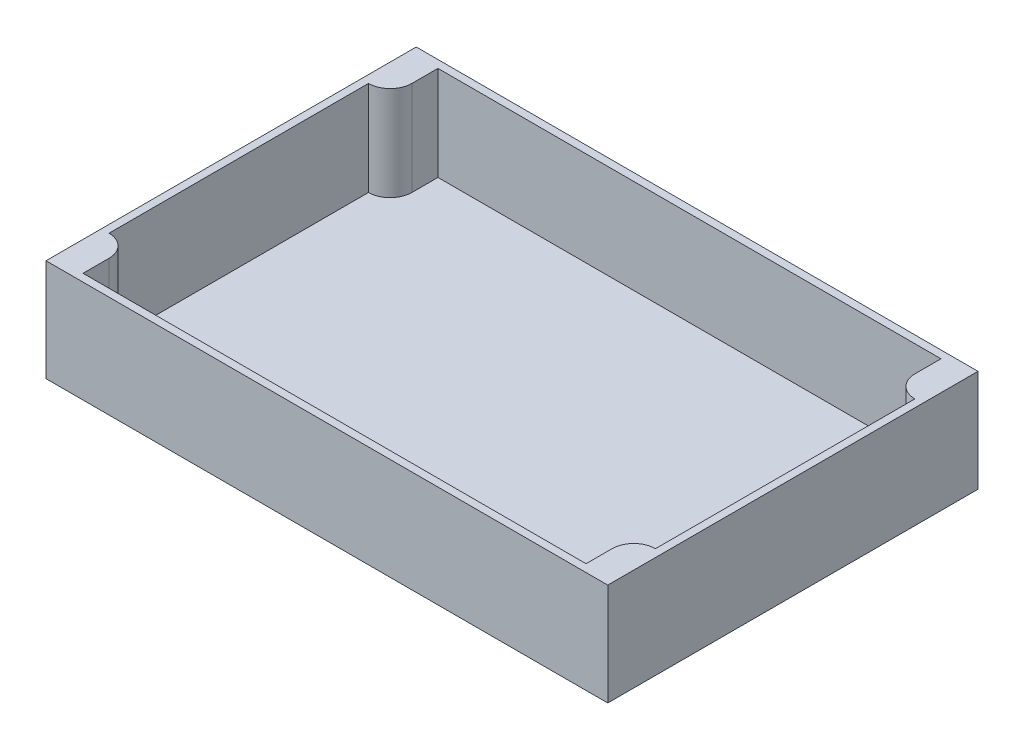
SolidWorks part; units mm, degrees
ref_plane "Front Plane" through (0, 0, 0) normal (0, 0, 1) x (1, 0, 0)
ref_plane "Top Plane" through (0, 0, 0) normal (0, 1, 0) x (1, 0, 0)
ref_plane "Right Plane" through (0, 0, 0) normal (1, 0, 0) x (0, 0, -1)
sketch "Sketch1" plane through (0, 0, 0) normal (0, 1, 0) x (1, 0, 0)
  line L1 (0, 0) -> (220, 0)
  line L2 (0, 0) -> (0, 145)
  line L3 (0, 145) -> (220, 145)
  line L4 (220, 0) -> (220, 145)
  dimension "D1" = 145
  dimension "D2" = 220
extrude "Boss-Extrude1" add sketch "Sketch1" along normal blind 3
sketch "Sketch2" plane through (0, 3, 0) normal (0, 1, 0) x (1, 0, 0)
  line L9 (0, 0) -> (0, 145)
  line L10 (0, 72.5) -> (3, 72.5) construction
  line L11 (3, 123.3) -> (3, 21.7)
  line L12 (11.5, 13.2) -> (11.5, 3)
  line L13 (0, 145) -> (0, 0) construction
  line L14 (0, 0) -> (220, 0) construction
  line L18 (11.5, 3) -> (208.5, 3)
  line L19 (110, 3) -> (110, 0) construction
  line L24 (220, 0) -> (0, 0)
  line L25 (110, 142) -> (110, 145) construction
  line L26 (220, 145) -> (0, 145)
  line L27 (11.5, 142) -> (208.5, 142)
  line L28 (11.5, 131.8) -> (11.5, 142)
  line L29 (220, 72.5) -> (217, 72.5) construction
  line L30 (208.5, 131.8) -> (208.5, 142)
  line L31 (208.5, 13.2) -> (208.5, 3)
  line L32 (217, 123.3) -> (217, 21.7)
  line L33 (220, 0) -> (220, 145)
  arc A4 (3, 21.7) -> (11.5, 13.2) centre (3, 13.2) cw
  arc A5 (3, 123.3) -> (11.5, 131.8) centre (3, 131.8) ccw
  arc A6 (217, 123.3) -> (208.5, 131.8) centre (217, 131.8) cw
  arc A7 (217, 21.7) -> (208.5, 13.2) centre (217, 13.2) ccw
  point P21 (0, 72.5)
  point P24 (110, 0)
  dimension "D1" = 3
  dimension "D2" = 8.5
  dimension "D3" = 18.7
extrude "Boss-Extrude2" add sketch "Sketch2" along direction (0, -1, 0) on the side of the normal offset from surface (37 mm away) 40
